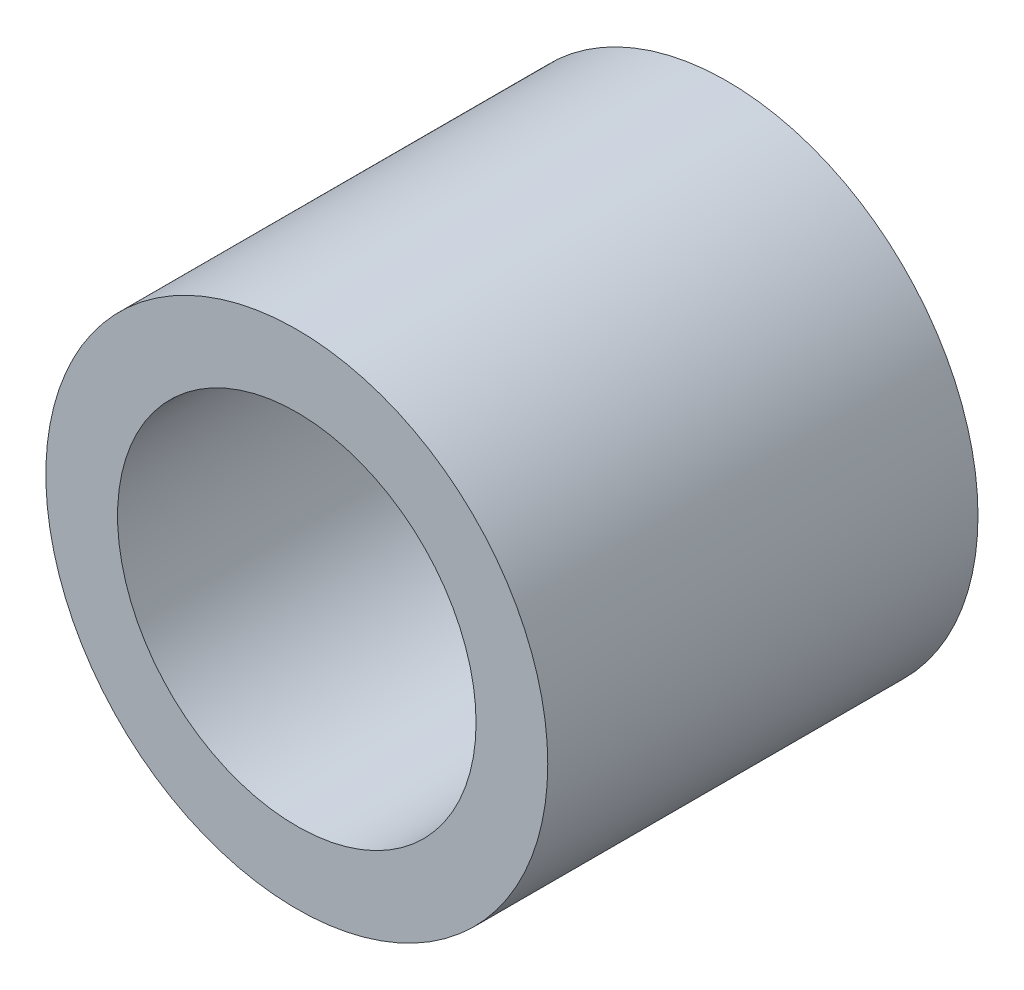
SolidWorks part; units mm, degrees
ref_plane "Front Plane" through (0, 0, 0) normal (0, 0, 1) x (1, 0, 0)
ref_plane "Top Plane" through (0, 0, 0) normal (0, 1, 0) x (1, 0, 0)
ref_plane "Right Plane" through (0, 0, 0) normal (1, 0, 0) x (0, 0, -1)
sketch "Sketch1" plane through (0, 0, 0) normal (0, 0, 1) x (1, 0, 0)
  circle A0 centre (0, 0) radius 3.5
  circle A1 centre (0, 0) radius 2.5
  dimension "D1" = 7
  dimension "D2" = 5
extrude "Boss-Extrude1" add sketch "Sketch1" along normal blind 6
